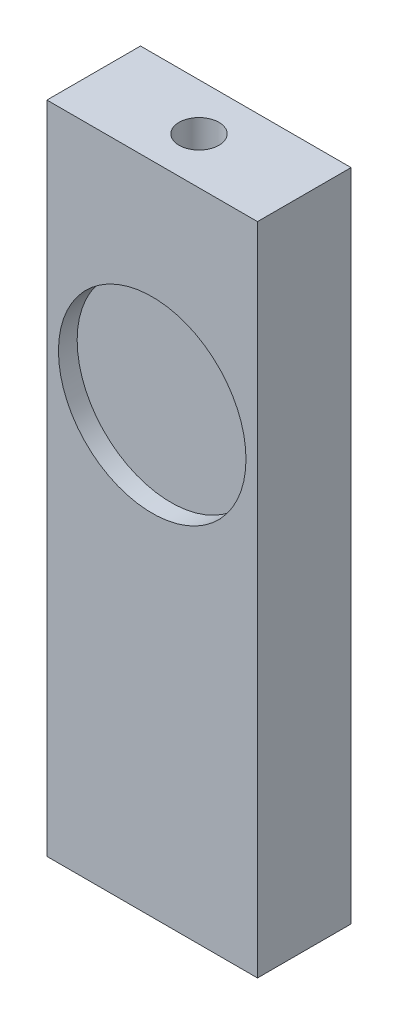
SolidWorks part; units mm, degrees
ref_plane "Front" through (0, 0, 0) normal (0, 0, 1) x (1, 0, 0)
ref_plane "Top" through (0, 0, 0) normal (0, 1, 0) x (1, 0, 0)
ref_plane "Right" through (0, 0, 0) normal (1, 0, 0) x (0, 0, -1)
sketch "Sketch1" plane through (0, 0, 0) normal (0, 1, 0) x (1, 0, 0)
  line L1 (-53.1168, 36.7917) -> (-38.8293, 36.7917)
  line L2 (-53.1168, 36.7917) -> (-53.1168, 30.4417)
  line L3 (-53.1168, 30.4417) -> (-38.8293, 30.4417)
  line L4 (-38.8293, 36.7917) -> (-38.8293, 30.4417)
  dimension "D1" = 14.2875
  dimension "D2" = 6.35
extrude "Extrude1" add sketch "Sketch1" along normal blind 44.45
sketch "Sketch6" plane through (0, 0, -30.4417) normal (0, 0, 1) x (1, 0, 0)
  line L0 (-53.1168, 44.45) -> (-38.8293, 44.45) construction
  line L1 (-38.8293, 44.45) -> (-38.8293, 0) construction
  circle A0 centre (-45.9731, 30.099) radius 6.3627
  dimension "D1" = 14.351
  dimension "D2" = 7.1437
extrude "Cut-Extrude2" cut sketch "Sketch6" against normal blind 1.27
hole_wizard "#6-32 Tapped Hole1" positions "3DSketch1" profile "Sketch7" tap size "#6-32" standard "Ansi Inch"
sketch3d "3DSketch1"
  line L0 (-53.1168, 0, -30.4417) -> (-38.8293, 0, -30.4417) construction
  line L1 (-38.8293, 0, -30.4417) -> (-38.8293, 0, -36.7917) construction
  line L2 (-53.1168, 44.45, -36.7917) -> (-53.1168, 44.45, -30.4417) construction
  line L3 (-53.1168, 44.45, -30.4417) -> (-38.8293, 44.45, -30.4417) construction
  point P0 (-45.9731, 44.45, -33.6167)
  point P2 (-45.9731, 0, -33.6167)
  dimension "D1" = 3.175
  dimension "D2" = 7.1437
  dimension "D3" = 7.1437
  dimension "D4" = 3.175
sketch "Sketch7" plane through (-45.9731, 44.45, -33.6167) normal (1, 0, 0) x (0, 0, 1)
  line L0 (0, 0) -> (0, 10.2107)
  line L1 (0, 10.2107) -> (1.3525, 9.398)
  line L2 (1.3525, 9.398) -> (1.3525, 0)
  line L5 (1.3525, 0) -> (0, 0)
  line L10 (0, 10.2107) -> (-1.3526, 9.398) construction
  line L11 (0, -6.35) -> (0, 107.95) construction
  dimension "Tap Drill Dia." = 2.7051
  dimension "Tap Drill Depth" = 9.398
  dimension "Drill Angle" = 118
cosmetic thread "Hole Thread1"
cosmetic thread "Hole Thread2"
